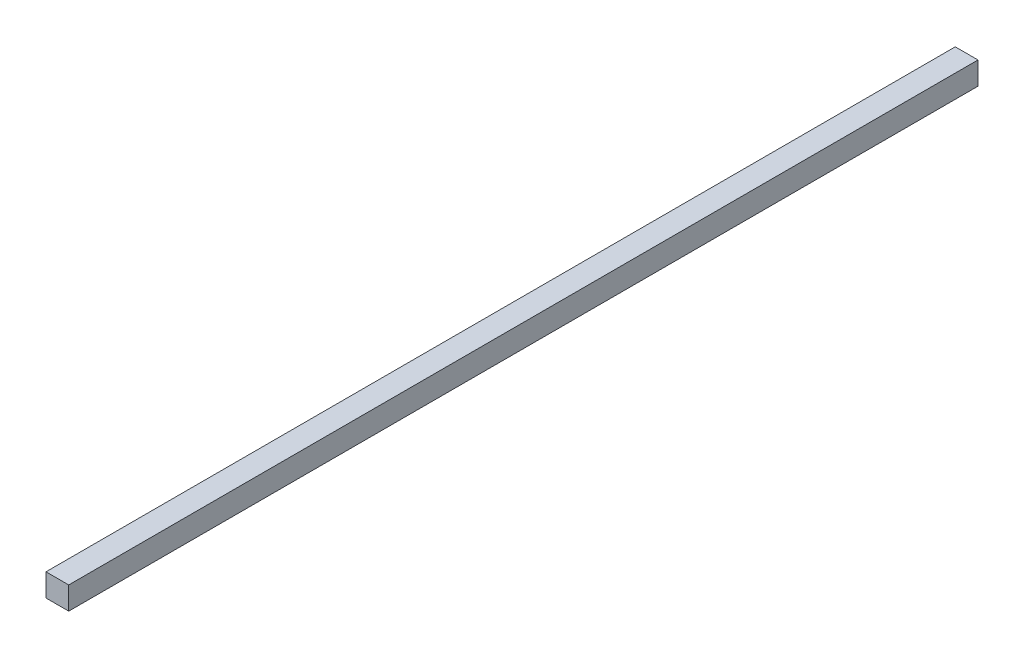
SolidWorks part; units mm, degrees
ref_plane "前视基准面" through (0, 0, 0) normal (0, 0, 1) x (1, 0, 0)
ref_plane "上视基准面" through (0, 0, 0) normal (0, 1, 0) x (1, 0, 0)
ref_plane "右视基准面" through (0, 0, 0) normal (1, 0, 0) x (0, 0, -1)
sketch "草图1" plane through (0, 0, 0) normal (0, 0, 1) x (1, 0, 0)
  line L1 (-10, -10) -> (10, -10)
  line L2 (-10, -10) -> (-10, 10)
  line L3 (-10, 10) -> (10, 10)
  line L4 (10, -10) -> (10, 10)
  line L5 (-10, -10) -> (10, 10) construction
  line L6 (-10, 10) -> (10, -10) construction
  point P0 (0, 0)
  dimension "D1" = 20
  dimension "D2" = 20
extrude "凸台-拉伸1" add sketch "草图1" along normal blind 800
